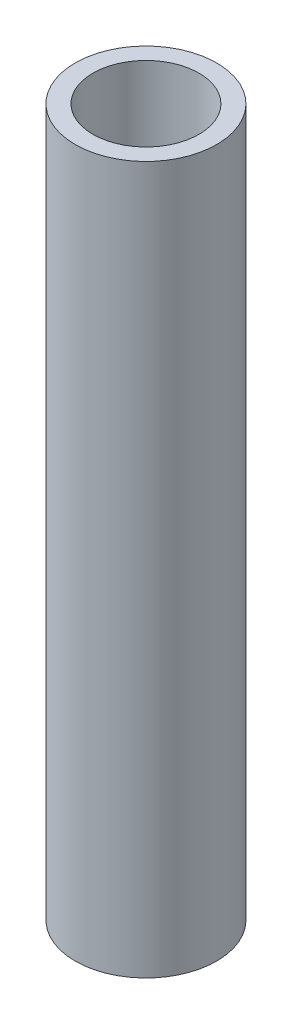
SolidWorks part; units mm, degrees
ref_plane "Front Plane" through (0, 0, 0) normal (0, 0, 1) x (1, 0, 0)
ref_plane "Top Plane" through (0, 0, 0) normal (0, 1, 0) x (1, 0, 0)
ref_plane "Right Plane" through (0, 0, 0) normal (1, 0, 0) x (0, 0, -1)
sketch "Sketch1" plane through (0, 0, 0) normal (0, 1, 0) x (1, 0, 0)
  circle A0 centre (0, 0) radius 20
  circle A1 centre (0, 0) radius 15
extrude "Boss-Extrude1" add sketch "Sketch1" along normal blind 200
ref_plane "Plane1" through (20, 0, 0) normal (1, 0, 0) x (0, 0, -1)
